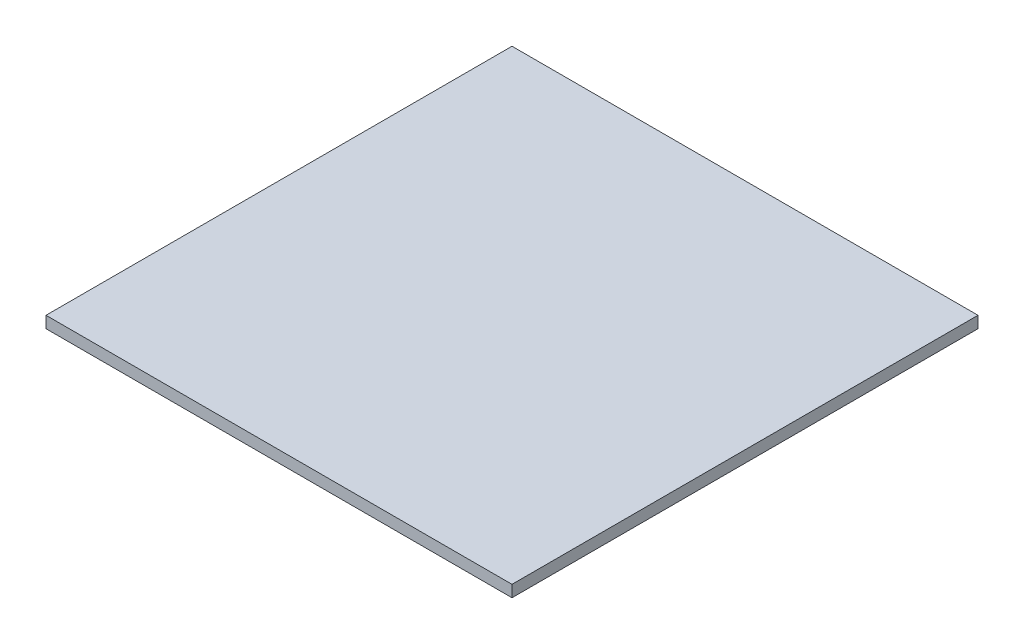
SolidWorks part; units mm, degrees
ref_plane "前视基准面" through (0, 0, 0) normal (0, 0, 1) x (1, 0, 0)
ref_plane "上视基准面" through (0, 0, 0) normal (0, 1, 0) x (1, 0, 0)
ref_plane "右视基准面" through (0, 0, 0) normal (1, 0, 0) x (0, 0, -1)
sketch "草图1" plane through (0, 0, 0) normal (0, 1, 0) x (1, 0, 0)
  line L1 (-25, -25) -> (25, -25)
  line L2 (-25, -25) -> (-25, 25)
  line L3 (-25, 25) -> (25, 25)
  line L4 (25, -25) -> (25, 25)
  line L5 (-25, -25) -> (25, 25) construction
  line L6 (-25, 25) -> (25, -25) construction
  point P0 (0, 0)
  dimension "D1" = 50
  dimension "D2" = 50
extrude "凸台-拉伸1" add sketch "草图1" along normal blind 1.25
